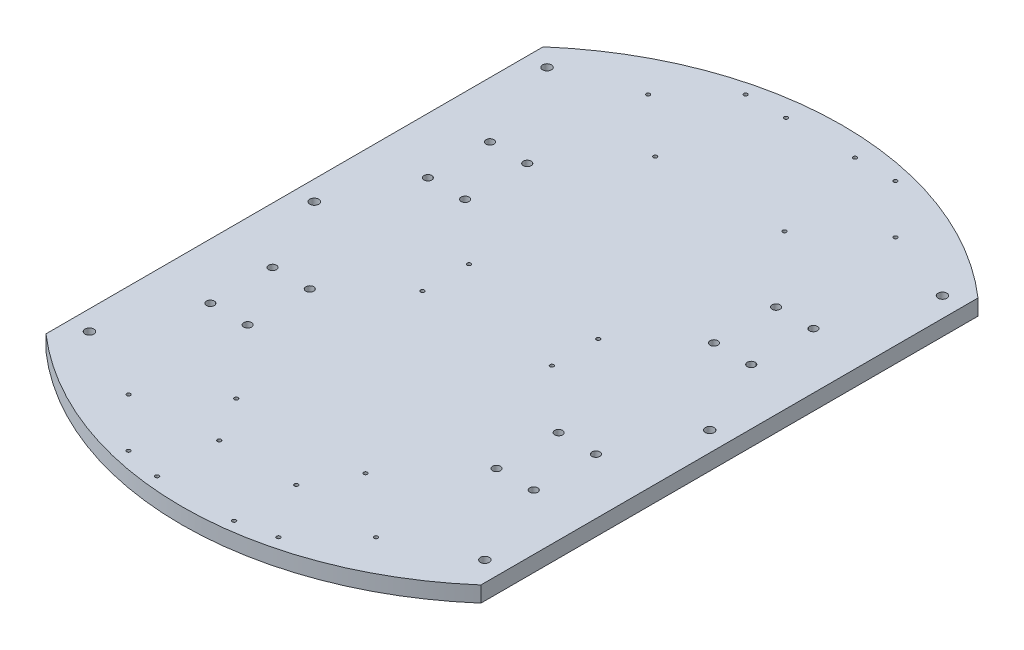
SolidWorks part; units mm, degrees
ref_plane "Front Plane" through (0, 0, 0) normal (0, 0, 1) x (1, 0, 0)
ref_plane "Top Plane" through (0, 0, 0) normal (0, 1, 0) x (1, 0, 0)
ref_plane "Right Plane" through (0, 0, 0) normal (1, 0, 0) x (0, 0, -1)
sketch "Sketch1" plane through (0, 0, 0) normal (0, 1, 0) x (1, 0, 0)
  line L0 (100.12, 112.41) -> (100.12, 62.41) construction
  line L7 (175, -200) -> (-175, -200) construction
  line L16 (175, -200) -> (175, 200)
  line L21 (175, 200) -> (-175, 200) construction
  line L22 (-175, -200) -> (-175, 200)
  line L23 (175, -200) -> (-175, 200) construction
  line L24 (175, 200) -> (-175, -200) construction
  line L25 (-175, 200) -> (175, 200) construction
  line L26 (-175, 200) -> (-175, 174.6) construction
  line L27 (-175, 174.6) -> (175, 174.6) construction
  line L28 (175, 200) -> (175, 174.6) construction
  line L29 (-175, -200) -> (175, -200) construction
  line L30 (-175, -200) -> (-175, -174.6) construction
  line L31 (-175, -174.6) -> (175, -174.6) construction
  line L32 (175, -200) -> (175, -174.6) construction
  line L33 (-175, 200) -> (-146.42, 200) construction
  line L34 (-175, 200) -> (-175, -200) construction
  line L35 (-175, -200) -> (-146.42, -200) construction
  line L36 (-146.42, 200) -> (-146.42, -200) construction
  line L37 (175, 200) -> (146.42, 200) construction
  line L38 (175, 200) -> (175, -200) construction
  line L39 (175, -200) -> (146.42, -200) construction
  line L40 (146.42, 200) -> (146.42, -200) construction
  line L41 (-175, -12.7) -> (175, -12.7) construction
  line L42 (-175, -12.7) -> (-175, 12.7) construction
  line L43 (-175, 12.7) -> (175, 12.7) construction
  line L44 (175, -12.7) -> (175, 12.7) construction
  line L45 (-175, -12.7) -> (175, 12.7) construction
  line L46 (-175, 12.7) -> (175, -12.7) construction
  line L47 (100.12, 112.41) -> (130.12, 112.41) construction
  line L48 (130.12, 112.41) -> (130.12, 62.41) construction
  line L50 (100.12, 62.41) -> (130.12, 62.41) construction
  line L52 (100.12, 112.41) -> (115.12, 87.41) construction
  line L54 (115.12, 87.41) -> (100.12, 62.41) construction
  line L55 (130.12, 112.41) -> (115.12, 87.41) construction
  line L56 (115.12, 87.41) -> (130.12, 62.41) construction
  line L68 (0, 200) -> (0, -200) construction
  line L69 (-99.51, 209.02) -> (-60.2656, 248.2644) construction
  line L70 (-27.75, 248.2644) -> (27.75, 248.2644) construction
  line L71 (99.51, 209.02) -> (60.2656, 248.2644) construction
  line L72 (-175, 0) -> (175, 0) construction
  line L75 (-53.36, 168.6) -> (50.74, 168.6) construction
  line L76 (-53.36, 168.6) -> (-53.36, 18.7) construction
  line L77 (-53.36, 18.7) -> (50.74, 18.7) construction
  line L78 (50.74, 168.6) -> (50.74, 18.7) construction
  line L79 (-53.36, -18.7) -> (50.74, -18.7) construction
  line L80 (-53.36, -168.6) -> (-53.36, -18.7) construction
  line L81 (-53.36, -168.6) -> (50.74, -168.6) construction
  line L82 (50.74, -168.6) -> (50.74, -18.7) construction
  line L83 (-28, -201.5745) -> (28, -201.5745) construction
  line L84 (0, -201.5745) -> (0, -265.7536) construction
  line L85 (-28, -201.5745) -> (-28, -207.5745) construction
  line L86 (-28, -207.5745) -> (-28, -251.5745) construction
  line L87 (-31, -251.5745) -> (-28, -251.5745) construction
  line L88 (-28, -201.5745) -> (-31, -201.5745) construction
  line L89 (-28, -257.5745) -> (-31, -257.5745) construction
  line L90 (-28, -207.5745) -> (-31, -207.5745) construction
  line L91 (-28, -251.5745) -> (-28, -257.5745) construction
  line L92 (-28, -257.5745) -> (-28, -264.2745) construction
  line L93 (28, -251.5745) -> (28, -257.5745) construction
  line L94 (28, -201.5745) -> (28, -207.5745) construction
  line L95 (28, -257.5745) -> (28, -264.2745) construction
  line L96 (28, -207.5745) -> (31, -207.5745) construction
  line L97 (28, -257.5745) -> (31, -257.5745) construction
  line L98 (28, -201.5745) -> (31, -201.5745) construction
  line L99 (31, -251.5745) -> (28, -251.5745) construction
  line L100 (28, -207.5745) -> (28, -251.5745) construction
  arc A5 (-175, -200) -> (175, -200) centre (0, 0) ccw
  arc A6 (-175, 200) -> (-175, -200) centre (0, 0) ccw construction
  arc A8 (175, -200) -> (175, 200) centre (0, 0) ccw construction
  arc A9 (175, 200) -> (-175, 200) centre (0, 0) ccw
  circle A14 centre (130.12, 112.41) radius 3.175
  circle A15 centre (130.12, 62.41) radius 3.175
  circle A16 centre (100.12, 112.41) radius 3.175
  circle A17 centre (100.12, 62.41) radius 3.175
  circle A23 centre (-130.12, 62.41) radius 3.175
  circle A24 centre (-100.12, 62.41) radius 3.175
  circle A25 centre (-100.12, 112.41) radius 3.175
  circle A26 centre (-130.12, 112.41) radius 3.175
  circle A27 centre (-130.12, -62.59) radius 3.175
  circle A28 centre (-100.12, -62.59) radius 3.175
  circle A29 centre (-100.12, -112.59) radius 3.175
  circle A30 centre (-130.12, -112.59) radius 3.175
  circle A31 centre (130.12, -62.59) radius 3.175
  circle A32 centre (100.12, -62.59) radius 3.175
  circle A33 centre (100.12, -112.59) radius 3.175
  circle A34 centre (130.12, -112.59) radius 3.175
  circle A35 centre (-99.51, 209.02) radius 1.5
  circle A36 centre (-60.2656, 248.2644) radius 1.5
  circle A37 centre (-27.75, 248.2644) radius 1.5
  circle A38 centre (27.75, 248.2644) radius 1.5
  circle A39 centre (60.2656, 248.2644) radius 1.5
  circle A40 centre (99.51, 209.02) radius 1.5
  circle A41 centre (-60.2656, -248.2644) radius 1.5
  circle A42 centre (99.51, -209.02) radius 1.5
  circle A43 centre (60.2656, -248.2644) radius 1.5
  circle A44 centre (-99.51, -209.02) radius 1.5
  circle A45 centre (-53.36, 168.6) radius 1.5
  circle A46 centre (50.74, 168.6) radius 1.5
  circle A47 centre (-53.36, 18.7) radius 1.5
  circle A48 centre (50.74, 18.7) radius 1.5
  circle A49 centre (50.74, -18.7) radius 1.5
  circle A50 centre (-53.36, -18.7) radius 1.5
  circle A51 centre (50.74, -168.6) radius 1.5
  circle A52 centre (-53.36, -168.6) radius 1.5
  arc A53 (-28, -264.2745) -> (28, -264.2745) centre (0, 0) ccw construction
  arc A54 (-31, -257.5745) -> (-31, -251.5745) centre (-31, -254.5745) cw construction
  arc A55 (31, -207.5745) -> (31, -201.5745) centre (31, -204.5745) ccw construction
  circle A56 centre (-31, -204.5745) radius 1.5
  circle A57 centre (-31, -254.5745) radius 1.5
  arc A58 (-31, -207.5745) -> (-31, -201.5745) centre (-31, -204.5745) cw construction
  circle A59 centre (31, -254.5745) radius 1.5
  circle A60 centre (31, -204.5745) radius 1.5
  arc A61 (31, -257.5745) -> (31, -251.5745) centre (31, -254.5745) ccw construction
  circle A62 centre (-159.12, 0) radius 3.5687
  circle A63 centre (-159.12, -180.95) radius 3.5687
  circle A64 centre (-159.12, 187.3) radius 3.5687
  circle A65 centre (159.12, -180.95) radius 3.5687
  circle A66 centre (159.12, 0) radius 3.5687
  circle A67 centre (159.12, 187.3) radius 3.5687
  point P17 (115.12, 87.41)
  point P62 (0, 248.2644)
  point P127 (-211.2882, 126.7387)
  point P128 (-159.12, 192.4427)
  dimension "D8" = 50
  dimension "D10" = 6.35
  dimension "D16" = 45
  dimension "D23" = 104.1
  dimension "D28" = 3
  dimension "D14" = 49.89
  dimension "D20" = 3
  dimension "D24" = 3
  dimension "D26" = 3
  dimension "D32" = 7.1374
  dimension "D33" = 12.7
  dimension "D1" = 350
  dimension "D2" = 400
  dimension "D3" = 25.4
  dimension "D4" = 28.58
  dimension "D5" = 25.4
  dimension "D6" = 28.58
  dimension "D7" = 25.4
  dimension "D9" = 30
  dimension "D11" = 49.71
  dimension "D12" = 16.3
  dimension "D13" = 2
  dimension "D15" = 55.5
  dimension "D17" = 75.49
  dimension "D18" = 9.02
  dimension "D19" = 55.5
  dimension "D21" = 95.68
  dimension "D22" = 149.9
  dimension "D25" = 6
  dimension "D27" = 50
  dimension "D29" = 6
  dimension "D30" = 62.7
  dimension "D31" = 28
  dimension "D34" = 12.7
  dimension "D35" = 12.7
extrude "Boss-Extrude1" add sketch "Sketch1" along normal blind 12.7
